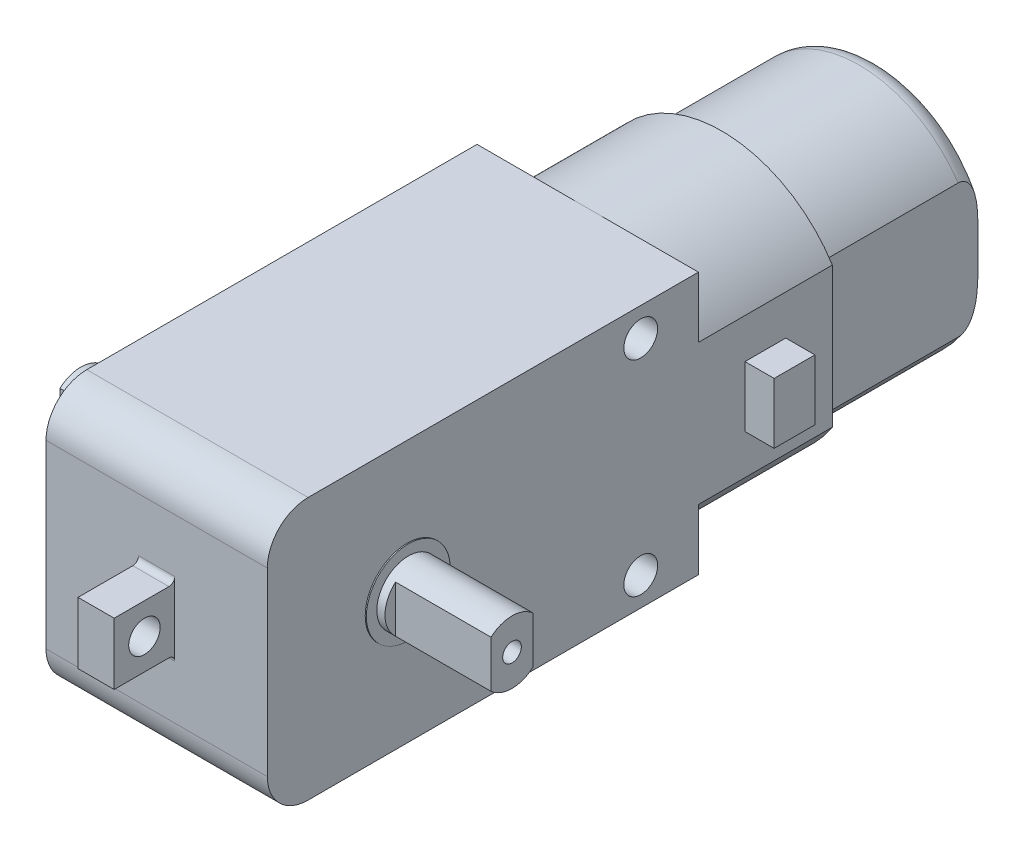
SolidWorks part; units mm, degrees
ref_plane "Front Plane" through (0, 0, 0) normal (0, 0, 1) x (1, 0, 0)
ref_plane "Top Plane" through (0, 0, 0) normal (0, 1, 0) x (1, 0, 0)
ref_plane "Right Plane" through (0, 0, 0) normal (1, 0, 0) x (0, 0, -1)
sketch "Sketch1" plane through (0, 0, 0) normal (1, 0, 0) x (0, 0, -1)
  line L0 (0, 0) -> (-38.2014, 0) construction
  line L2 (-37, -11.25) -> (0, -11.25)
  line L3 (-37, -11.25) -> (-37, 11.25)
  line L4 (-37, 11.25) -> (0, 11.25)
  line L5 (0, -11.25) -> (0, 11.25)
  line L6 (-37, -11.25) -> (0, 11.25) construction
  line L7 (-37, 11.25) -> (0, -11.25) construction
  point P3 (-18.5, 0)
  dimension "D1" = 22.5
  dimension "D2" = 37
extrude "Boss-Extrude1" add sketch "Sketch1" along normal blind 19
sketch "Sketch2" plane through (0, 0, 37) normal (0, 0, 1) x (1, 0, 0)
  line L0 (9.5, 11.25) -> (9.5, -11.25) construction
  line L1 (19, 11.25) -> (0, 11.25) construction
  line L2 (19, -11.25) -> (0, -11.25) construction
  line L3 (0, 0) -> (19, 0) construction
  line L4 (19, 11.25) -> (19, -11.25) construction
  line L6 (7.95, -2.65) -> (11.05, -2.65)
  line L7 (7.95, -2.65) -> (7.95, 2.65)
  line L8 (7.95, 2.65) -> (11.05, 2.65)
  line L9 (11.05, -2.65) -> (11.05, 2.65)
  line L10 (7.95, -2.65) -> (11.05, 2.65) construction
  line L11 (7.95, 2.65) -> (11.05, -2.65) construction
  point P11 (9.5, 0)
  dimension "D1" = 3.1
  dimension "D2" = 5.3
extrude "Boss-Extrude2" add sketch "Sketch2" along normal blind 5.2
sketch "Sketch3" plane through (11.05, 0, 0) normal (1, 0, 0) x (0, 0, -1)
  line L0 (-42.2, 2.65) -> (-37, -2.65) construction
  line L1 (-42.2, -2.65) -> (-37, 2.65) construction
  line L2 (-37, 11.25) -> (-37, -11.25) construction
  line L3 (-37, -2.65) -> (-37, 2.65) construction
  line L4 (-42.2, 2.65) -> (-37, 2.65) construction
  circle A0 centre (-39.6, 0) radius 1.35
  dimension "D1" = 2.7
extrude "Cut-Extrude1" cut sketch "Sketch3" against normal through all
fillet "Fillet1" radius 3.5 2 edges at (9.5, -11.25, 37) (9.5, 11.25, 37)
sketch "Sketch4" plane through (19, 0, 0) normal (1, 0, 0) x (0, 0, -1)
  line L0 (-25, 11.25) -> (-25, -11.25) construction
  line L1 (0, 11.25) -> (-33.5, 11.25) construction
  line L2 (-33.5, -11.25) -> (0, -11.25) construction
  line L3 (-37, 0) -> (0, 0) construction
  line L4 (-37, 7.75) -> (-37, -7.75) construction
  circle A0 centre (-25, 0) radius 3.6
  dimension "D2" = 7.2
  dimension "D1" = 12
extrude "Boss-Extrude3" add sketch "Sketch4" along normal blind 0.1
sketch "Sketch5" plane through (0, 0, 0) normal (-1, 0, 0) x (0, 0, 1)
  circle A0 centre (25, 0) radius 3.6 construction
  circle A1 centre (25, 0) radius 3.6
extrude "Boss-Extrude4" add sketch "Sketch5" along normal blind 0.1
sketch "Sketch6" plane through (19.1, 0, 0) normal (1, 0, 0) x (0, 0, -1)
  circle A0 centre (-25, 0) radius 2.7
  dimension "D1" = 5.4
extrude "Boss-Extrude5" add sketch "Sketch6" along normal blind 8.9
sketch "Sketch7" plane through (-0.1, 0, 0) normal (-1, 0, 0) x (0, 0, 1)
  circle A0 centre (25, 0) radius 2.7 construction
  circle A1 centre (25, 0) radius 2.7
extrude "Boss-Extrude6" add sketch "Sketch7" along normal blind 8.9
fillet "Fillet2" radius 0.5 2 edges at (9.5, -2.65, 37) (9.5, 2.65, 37)
sketch "Sketch8" plane through (28, 0, 0) normal (1, 0, 0) x (0, 0, -1)
  line L0 (-26.8, 2.0125) -> (-26.8, -2.0125)
  line L2 (-23.2, -2.0125) -> (-23.2, 2.0125)
  circle A0 centre (-25, 0) radius 2.7 construction
  circle A1 centre (-25, 0) radius 2.7
  circle M3 centre (-25, 0) radius 2.7
  dimension "D1" = 3.6
extrude "Cut-Extrude2" cut sketch "Sketch8" against normal blind 8.2 contours L0 M3 | L2 M3
sketch "Sketch9" plane through (-9, 0, 0) normal (-1, 0, 0) x (0, 0, 1)
  line L0 (26.8, 2.0125) -> (26.8, -2.0125) construction
  line L1 (23.2, -2.0125) -> (23.2, 2.0125) construction
  line L2 (26.8, 2.0125) -> (26.8, -2.0125)
  line L3 (23.2, -2.0125) -> (23.2, 2.0125)
  circle A0 centre (25, 0) radius 2.7 construction
  circle A1 centre (25, 0) radius 2.7
  circle M1 centre (25, 0) radius 2.7
extrude "Cut-Extrude3" cut sketch "Sketch9" against normal blind 8.2 contours L3 M1 | L2 M1
hole_wizard "M2x0.4 Tapped Hole1" positions "Sketch11" profile "Sketch10" tap size "M2x0.4" standard "ANSI Metric"
sketch "Sketch11" plane through (28, 0, 0) normal (1, 0, 0) x (0, 0, -1)
  point P0 (-25, 0)
sketch "Sketch10" plane through (28, 0, 25) normal (0, 1, 0) x (0, 0, -1)
  line L0 (0, 0) -> (0, 5.6807)
  line L1 (0, 5.6807) -> (0.8, 5.2)
  line L2 (0.8, 5.2) -> (0.8, 0)
  line L5 (0.8, 0) -> (0, 0)
  line L10 (0, 5.6807) -> (-0.8, 5.2) construction
  line L11 (0, -6.35) -> (0, 107.95) construction
  dimension "Tap Drill Dia." = 1.6
  dimension "Tap Drill Depth" = 5.2
  dimension "Drill Angle" = 118
cosmetic thread "Hole Thread1" parameters "D1"=4, "D2"=2
hole_wizard "M2x0.4 Tapped Hole2" positions "Sketch15" profile "Sketch14" tap size "M2x0.4" standard "ANSI Metric"
sketch "Sketch15" plane through (-9, 0, 0) normal (-1, 0, 0) x (0, 0, 1)
  point P0 (25, 0)
sketch "Sketch14" plane through (-9, 0, 25) normal (0, 1, 0) x (0, 0, 1)
  line L0 (0, 0) -> (0, 5.6807)
  line L1 (0, 5.6807) -> (0.8, 5.2)
  line L2 (0.8, 5.2) -> (0.8, 0)
  line L5 (0.8, 0) -> (0, 0)
  line L10 (0, 5.6807) -> (-0.8, 5.2) construction
  line L11 (0, -6.35) -> (0, 107.95) construction
  dimension "Tap Drill Dia." = 1.6
  dimension "Tap Drill Depth" = 5.2
  dimension "Drill Angle" = 118
cosmetic thread "Hole Thread2" parameters "D1"=4, "D2"=2
sketch "Sketch16" plane through (0, 0, 0) normal (-1, 0, 0) x (0, 0, 1)
  line L0 (0, 0) -> (21.4, 0) construction
  circle A0 centre (25, 0) radius 3.6 construction
  circle A1 centre (13.75, 0) radius 1.95
  circle A4 centre (25, 0) radius 3.6 construction
  dimension "D1" = 3.9
  dimension "D2" = 5.7
extrude "Boss-Extrude7" add sketch "Sketch16" along normal blind 2
sketch "Sketch17" plane through (0, 0, 0) normal (0, 0, -1) x (-1, 0, 0)
  line L0 (-19, 11.25) -> (0, -11.25) construction
  line L1 (-19, -11.25) -> (0, 11.25) construction
  line L2 (-19, -11.25) -> (-19, 11.25) construction
  line L3 (-19, -11.25) -> (-19, 11.25)
  line L6 (-1.3, -11.25) -> (-1.3, 11.25)
  line L7 (-1.3, -11.25) -> (-1.3, 11.25)
  circle A0 centre (-9.5, 0) radius 11.25
  dimension "D1" = 1.3
extrude "Boss-Extrude8" add sketch "Sketch17" along normal blind 11.5 contours L7 A0 L3
sketch "Sketch18" plane through (19, 0, 0) normal (1, 0, 0) x (0, 0, -1)
  line L0 (11.5, 0) -> (0, 0) construction
  line L1 (11.5, 6.026) -> (11.5, -6.026) construction
  line L3 (4, -2.6) -> (7.5, -2.6)
  line L4 (4, -2.6) -> (4, 2.6)
  line L5 (4, 2.6) -> (7.5, 2.6)
  line L6 (7.5, -2.6) -> (7.5, 2.6)
  line L7 (4, -2.6) -> (7.5, 2.6) construction
  line L8 (4, 2.6) -> (7.5, -2.6) construction
  point P5 (5.75, 0)
  dimension "D1" = 4
  dimension "D2" = 5.2
  dimension "D3" = 3.5
extrude "Boss-Extrude9" add sketch "Sketch18" along normal blind 2.5
sketch "Sketch19" plane through (1.3, 0, 0) normal (-1, 0, 0) x (0, 0, 1)
  line L0 (-7.5, 2.6) -> (-4, 2.6) construction
  line L1 (-4, 2.6) -> (-4, -2.6) construction
  line L2 (-4, -2.6) -> (-7.5, -2.6) construction
  line L3 (-7.5, -2.6) -> (-7.5, 2.6) construction
  line L4 (-7.5, 2.6) -> (-4, 2.6)
  line L5 (-4, 2.6) -> (-4, -2.6)
  line L6 (-4, -2.6) -> (-7.5, -2.6)
  line L7 (-7.5, -2.6) -> (-7.5, 2.6)
extrude "Boss-Extrude10" add sketch "Sketch19" along normal blind 2.5
sketch "Sketch20" plane through (0, 0, -11.5) normal (0, 0, -1) x (-1, 0, 0)
  line L20 (-18, 6.026) -> (-18, -6.026)
  line L21 (-18, 5.7282) -> (-18, -5.7282)
  line L23 (-2.3, -7.7021) -> (-2.3, 7.7021)
  line L24 (-2.3, -7.2954) -> (-2.3, 7.2954)
  arc A30 (-2.0289, 7.0175) -> (-18.1556, 5.4903) centre (-9.5, 0) ccw
  arc A31 (-2.3, 7.2954) -> (-18, 5.7282) centre (-9.5, 0) ccw
  arc A34 (-18.1556, -5.4903) -> (-2.0289, -7.0175) centre (-9.5, 0) ccw
  arc A35 (-18, -5.7282) -> (-2.3, -7.2954) centre (-9.5, 0) ccw
  dimension "D1" = 1
  dimension "D2" = 1
  dimension "D3" = 1
  dimension "D4" = 1
extrude "Boss-Extrude11" add sketch "Sketch20" along normal blind 13.5
fillet "Fillet3" radius 1.7 2 edges at (10.5181, -10.1993, -25) (10.5181, 10.1993, -25)
sketch "Sketch21" plane through (0, 0, -25) normal (0, 0, -1) x (-1, 0, 0)
  line L0 (-5.5, 3) -> (-5.5, -3)
  circle A0 centre (-9.5, 0) radius 5
  dimension "D1" = 10
  dimension "D2" = 9
extrude "Boss-Extrude12" add sketch "Sketch21" along normal blind 2 contours L0 A0
sketch "Sketch22" [suppressed] plane through (0, 0, -27) normal (0, 0, -1) x (-1, 0, 0)
  circle A0 centre (-9.5, 0) radius 1
  arc A1 (-5.5, 3) -> (-5.5, -3) centre (-9.5, 0) ccw construction
  dimension "D1" = 2
extrude "Boss-Extrude14" [suppressed] add sketch "Sketch22" along normal blind 1.5
sketch "Sketch23" [suppressed] plane through (0, 0, -25) normal (0, 0, -1) x (-1, 0, 0)
  line L0 (-9.5, 10.25) -> (-9.5, -11.25) construction
  line L1 (-7.9, 7) -> (-7.9, -7) construction
  line L2 (-11.1, 13.5) -> (-7.9, 13.5)
  line L3 (-11.1, 13.5) -> (-11.1, 7)
  line L4 (-11.1, 7) -> (-7.9, 7)
  line L5 (-7.9, 13.5) -> (-7.9, 7)
  line L6 (-11.1, 13.5) -> (-7.9, 7) construction
  line L7 (-11.1, 7) -> (-7.9, 13.5) construction
  line L8 (-11.1, -15.5) -> (-7.9, -15.5)
  line L9 (-11.1, -15.5) -> (-11.1, -7)
  line L10 (-11.1, -7) -> (-7.9, -7)
  line L11 (-7.9, -15.5) -> (-7.9, -7)
  line L12 (-11.1, -15.5) -> (-7.9, -7) construction
  line L13 (-11.1, -7) -> (-7.9, -15.5) construction
  line L14 (-9.5, 0) -> (-7.9, 7) construction
  line L16 (-9.5, 0) -> (-7.9, -7) construction
  arc A0 (-2.3, 7.2954) -> (-18, 5.7282) centre (-9.5, 0) ccw construction
  dimension "D1" = 14
  dimension "D2" = 3.2
extrude "Cut-Extrude4" [suppressed] cut sketch "Sketch23" against normal blind 6
sketch "Sketch24" plane through (0, -11.25, 0) normal (0, -1, 0) x (1, 0, 0)
  line L0 (19, 25) -> (0, 25) construction
  line L1 (19, 33.5) -> (19, 0) construction
  line L2 (0, 33.5) -> (0, 0) construction
  line L3 (28, 25) -> (19, 25) construction
  line L4 (28, 23.2) -> (28, 26.8) construction
ref_plane "Plane1" through (0, 0, 25) normal (0, 0, 1) x (-1, 0, 0)
sketch "Sketch25" plane through (19, 0, 0) normal (1, 0, 0) x (0, 0, -1)
  line L0 (-4.95, 11.25) -> (-4.95, -11.25) construction
  line L1 (0, 11.25) -> (-33.5, 11.25) construction
  line L2 (-33.5, -11.25) -> (0, -11.25) construction
  line L4 (0, 6.026) -> (0, 11.25) construction
  line L5 (-37, 7.75) -> (-37, -7.75) construction
  circle A0 centre (-4.95, 8.8) radius 1.45
  circle A1 centre (-4.95, -8.8) radius 1.45
  dimension "D1" = 2.9
  dimension "D2" = 14.7
  dimension "D5" = 3.5
  dimension "D3" = 1
  dimension "D4" = 1
  dimension "D6" = 30.6
extrude "Cut-Extrude5" cut sketch "Sketch25" against normal through all
